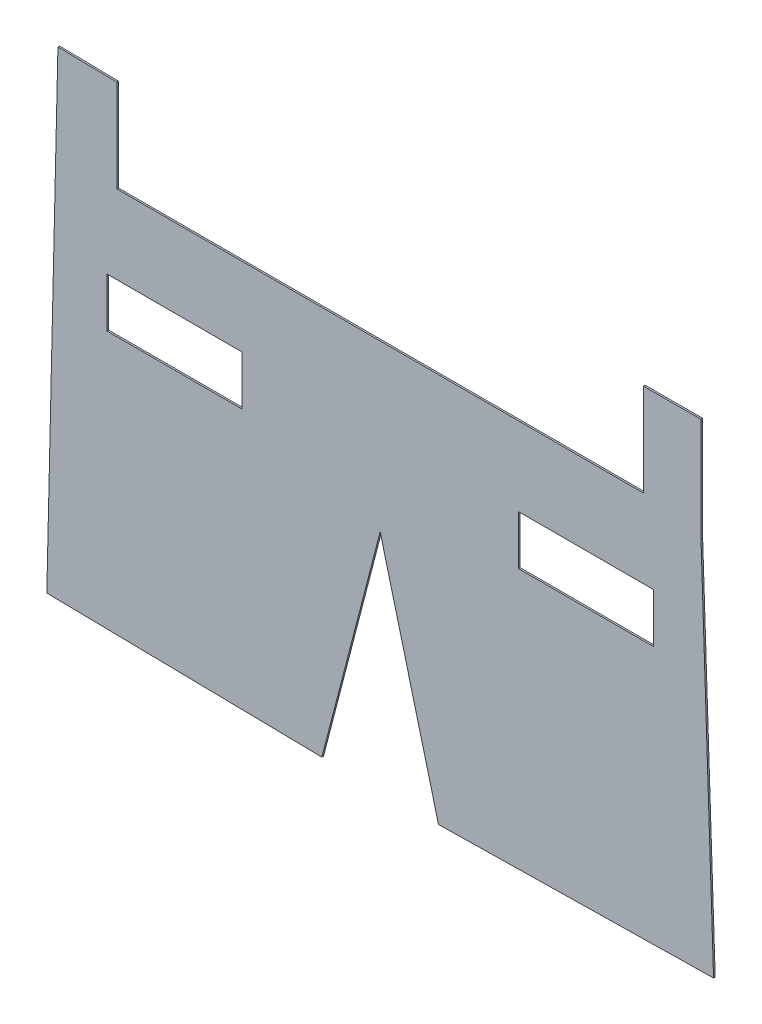
SolidWorks part; units mm, degrees
ref_plane "Alzado" through (0, 0, 0) normal (0, 0, 1) x (1, 0, 0)
ref_plane "Planta" through (0, 0, 0) normal (0, 1, 0) x (1, 0, 0)
ref_plane "Vista lateral" through (0, 0, 0) normal (1, 0, 0) x (0, 0, -1)
sketch "Model" plane through (0, 0, 0) normal (0, 0, 1) x (1, 0, 0)
  line L0 (50.1249, 24.6176) -> (50.1249, 19.6176)
  line L1 (50.8876, -3.1035) -> (34.1694, -3.3817)
  line L2 (10.3647, -3.1035) -> (27.083, -3.3817)
  line L3 (50.1249, 25.9284) -> (46.6262, 25.9176)
  line L4 (11.0404, 25.9785) -> (14.6262, 25.9176)
  line L5 (11.0404, 25.9785) -> (10.3647, -3.1035)
  line L6 (14.6262, 20.2957) -> (14.6262, 25.9176)
  line L7 (46.6262, 20.2957) -> (14.6262, 20.2957)
  line L8 (46.6262, 25.9176) -> (46.6262, 20.2957)
  line L9 (22.2262, 12.5176) -> (14.0262, 12.5176)
  line L10 (14.0262, 12.5176) -> (14.0262, 15.5176)
  line L11 (14.0262, 15.5176) -> (22.2262, 15.5176)
  line L12 (22.2262, 15.5176) -> (22.2262, 12.5176)
  line L13 (47.2262, 12.5176) -> (47.2262, 15.5176)
  line L14 (47.2262, 15.5176) -> (39.0262, 15.5176)
  line L15 (39.0262, 15.5176) -> (39.0262, 12.5176)
  line L16 (39.0262, 12.5176) -> (47.2262, 12.5176)
  line L17 (30.6262, 10.2504) -> (34.1694, -3.3817)
  line L18 (27.083, -3.3817) -> (30.6262, 10.2504)
  line L19 (50.8876, -3.1035) -> (50.1249, 19.6176)
  line L20 (50.1249, 24.6176) -> (50.1249, 25.9284)
  point P21 (0, 0)
extrude "Saliente-Extruir1" add sketch "Model" along normal blind 0.1
